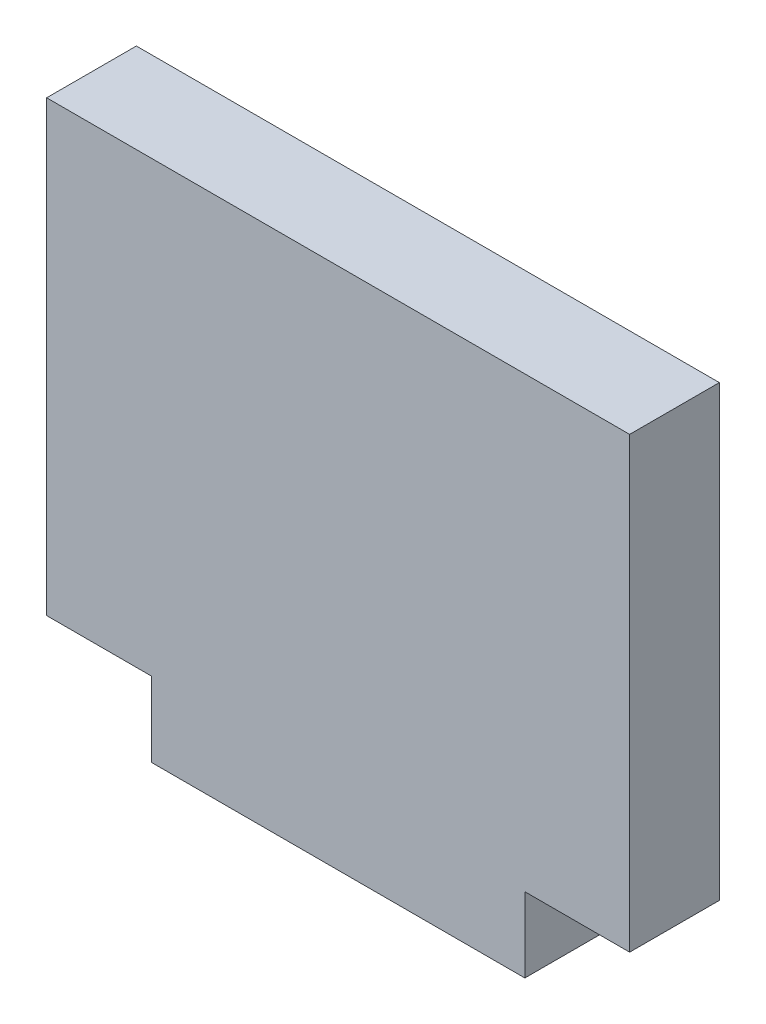
SolidWorks part; units mm, degrees
ref_plane "Plan de face" through (0, 0, 0) normal (0, 0, 1) x (1, 0, 0)
ref_plane "Plan de dessus" through (0, 0, 0) normal (0, 1, 0) x (1, 0, 0)
ref_plane "Plan de droite" through (0, 0, 0) normal (1, 0, 0) x (0, 0, -1)
sketch "Esquisse1" plane through (0, 0, 0) normal (0, 0, 1) x (1, 0, 0)
  line L1 (-18.9566, 19.723) -> (20.0434, 19.723)
  line L2 (-18.9566, 19.723) -> (-18.9566, -10.277)
  line L3 (-18.9566, -10.277) -> (20.0434, -10.277)
  line L4 (20.0434, 19.723) -> (20.0434, -10.277)
  line L5 (-11.9466, -10.277) -> (13.0334, -10.277)
  line L6 (-11.9466, -10.277) -> (-11.9466, -15.277)
  line L7 (-11.9466, -15.277) -> (13.0334, -15.277)
  line L8 (13.0334, -10.277) -> (13.0334, -15.277)
  dimension "D1" = 24.98
  dimension "D2" = 5
  dimension "D3" = 39
  dimension "D4" = 7.01
  dimension "D5" = 30
extrude "Boss.-Extru.1" add sketch "Esquisse1" along normal blind 6 contours L4 L1 L2 L3 | L8 L3 L6 L7
